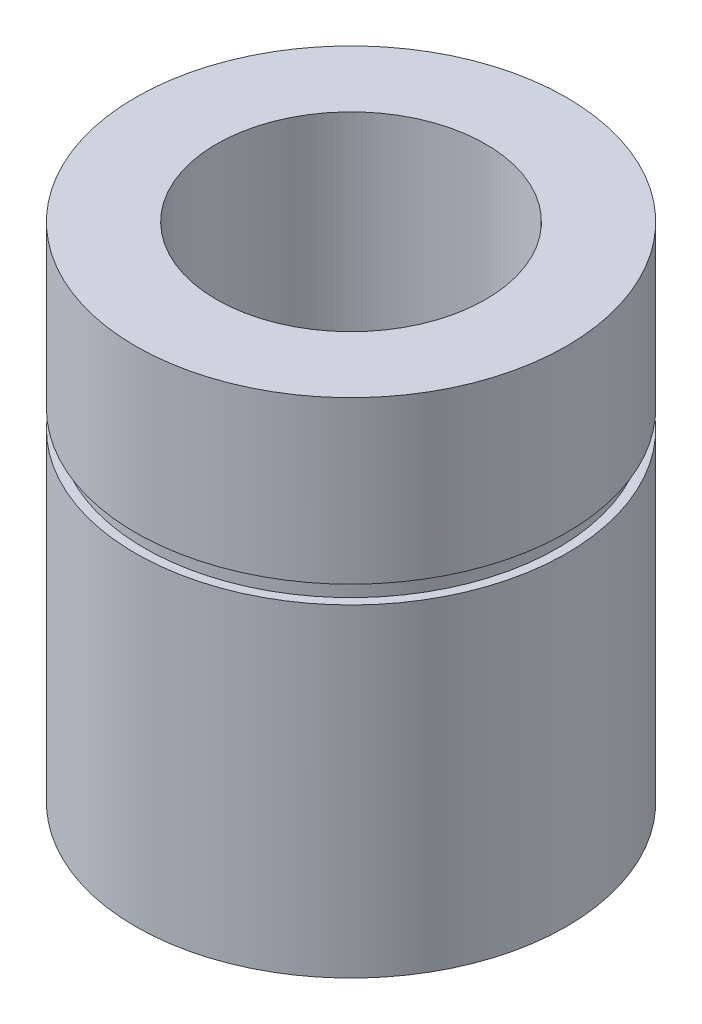
SolidWorks part; units mm, degrees
ref_plane "Vorne" through (0, 0, 0) normal (0, 0, 1) x (1, 0, 0)
ref_plane "Oben" through (0, 0, 0) normal (0, 1, 0) x (1, 0, 0)
ref_plane "Rechts" through (0, 0, 0) normal (1, 0, 0) x (0, 0, -1)
sketch "Skizze1" plane through (0, 0, 0) normal (0, 1, 0) x (1, 0, 0)
  circle A0 centre (0, 0) radius 7.5
  circle A1 centre (0, 0) radius 12
  dimension "D1" = 15
  dimension "D2" = 24
extrude "Aufsatz-Linear austragen1" add sketch "Skizze1" along normal blind 28
sketch "Skizze2" plane through (0, 28, 0) normal (0, -1, 0) x (1, 0, 0)
  circle A0 centre (0, 0) radius 12
  circle A1 centre (0, 0) radius 11.5
  dimension "D1" = 23
extrude "Schnitt-Linear austragen1" cut sketch "Skizze2" along normal blind 1 from offset 9
